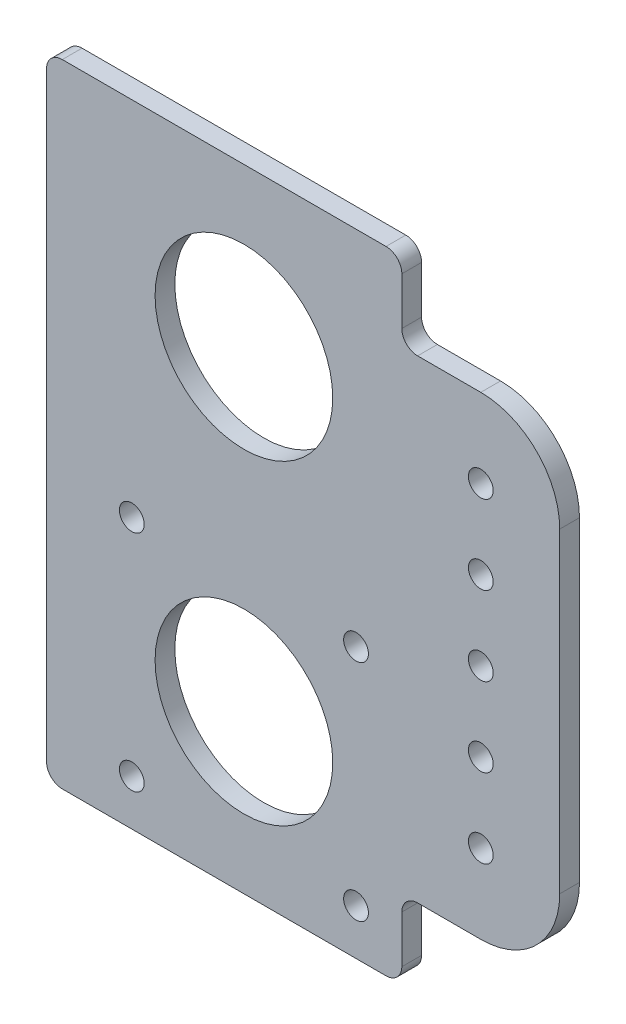
SolidWorks part; units mm, degrees
ref_plane "Front Plane" through (0, 0, 0) normal (0, 0, 1) x (1, 0, 0)
ref_plane "Top Plane" through (0, 0, 0) normal (0, 1, 0) x (1, 0, 0)
ref_plane "Right Plane" through (0, 0, 0) normal (1, 0, 0) x (0, 0, -1)
sketch "Sketch1" plane through (0, 0, 0) normal (0, 0, 1) x (1, 0, 0)
  line L0 (0, 50.8) -> (0, 0) construction
  line L1 (-31.75, 76.2) -> (50.8, 76.2)
  line L2 (-31.75, 76.2) -> (-31.75, -25.4)
  line L3 (-31.75, -25.4) -> (50.8, -25.4)
  line L4 (50.8, 76.2) -> (50.8, -25.4)
  line L5 (25.4, 76.2) -> (25.4, 63.5)
  line L6 (38.1, -12.7) -> (25.4, -12.7)
  line L7 (38.1, 63.5) -> (25.4, 63.5)
  line L8 (25.4, -12.7) -> (25.4, -25.4)
  circle A0 centre (0, 0) radius 14.2875
  circle A1 centre (-18.034, 18.034) radius 1.9939
  circle A2 centre (0, 0) radius 14.2875
  circle A3 centre (18.034, 18.034) radius 1.9939
  circle A4 centre (0, 0) radius 14.2875
  circle A5 centre (18.034, -18.034) radius 1.9939
  circle A6 centre (0, 0) radius 14.2875
  circle A7 centre (-18.034, -18.034) radius 1.9939
  circle A8 centre (0, 50.8) radius 14.2875
  circle A9 centre (38.1, 50.8) radius 1.9939
  circle A10 centre (38.1, 38.1) radius 1.9939
  circle A11 centre (38.1, 25.4) radius 1.9939
  circle A12 centre (38.1, 12.7) radius 1.9939
  circle A13 centre (38.1, 0) radius 1.9939
  arc A14 (50.8, 50.8) -> (38.1, 63.5) centre (38.1, 50.8) ccw
  arc A15 (50.8, 0) -> (38.1, -12.7) centre (38.1, 0) cw
  point P17 (0, 0)
  point P21 (0, 25.4)
  dimension "D1" = 28.575
  dimension "D2" = 3.9878
  dimension "D13" = 3.9878
  dimension "D16" = 28.575
  dimension "D3" = 18.034
  dimension "D4" = 18.034
  dimension "D6" = 50.8
  dimension "D7" = 50.8
  dimension "D8" = 50.8
  dimension "D9" = 31.75
  dimension "D10" = 50.8
  dimension "D11" = 25.4
  dimension "D12" = 12.7
  dimension "D14" = 25.4
  dimension "D15" = 5
  dimension "D5" = 4
extrude "Boss-Extrude1" add sketch "Sketch1" along normal blind 3.175
fillet "Fillet1" radius 2.54 6 edges at (25.4, -12.7, 1.5875) (25.4, -25.4, 1.5875) (-31.75, -25.4, 1.5875) (-31.75, 76.2, 1.5875) (25.4, 76.2, 1.5875) (25.4, 63.5, 1.5875)
